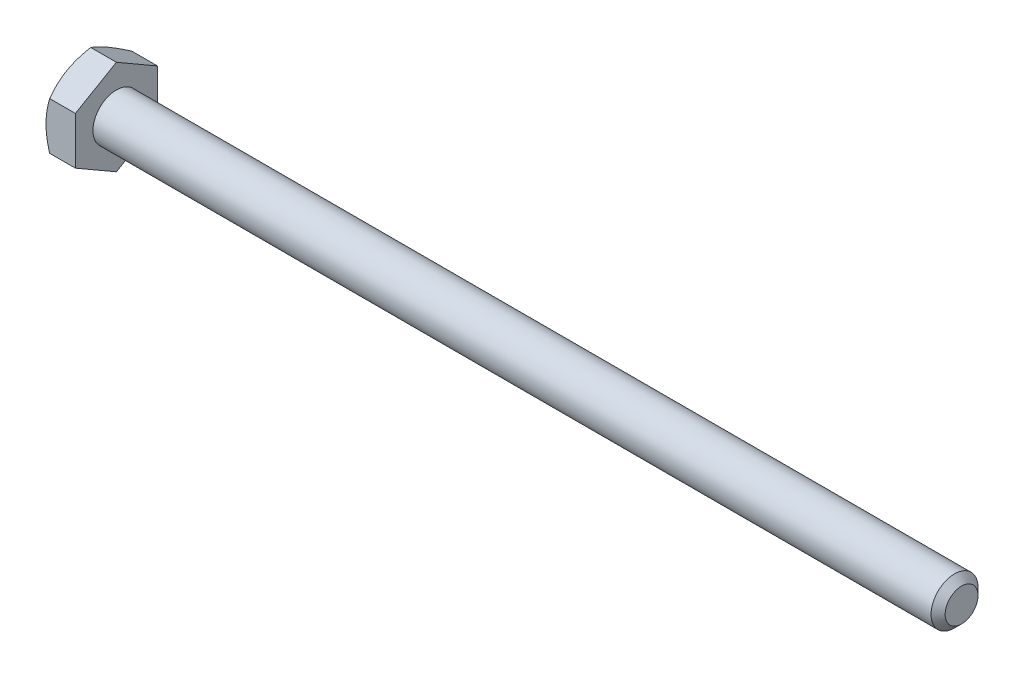
SolidWorks part; units mm, degrees
ref_plane "Front Plane" through (0, 0, 0) normal (0, 0, 1) x (1, 0, 0)
ref_plane "Top Plane" through (0, 0, 0) normal (0, 1, 0) x (1, 0, 0)
ref_plane "Right Plane" through (0, 0, 0) normal (1, 0, 0) x (0, 0, -1)
sketch "Sketch1" plane through (0, 0, 0) normal (0, 0, 1) x (1, 0, 0)
  line L0 (-59.1344, 0) -> (59.1344, 0) construction
  line L1 (59.1344, 3.175) -> (59.1344, -3.175) construction
  line L2 (-55.1656, 5.5562) -> (-55.1656, -5.5562) construction
  line L3 (-59.1344, 5.5562) -> (-59.1344, -5.5562) construction
  point P9 (-55.1656, 0)
  point P10 (54.6894, -3.175)
  dimension "D1" = 4.445
  dimension "Screw Dia" = 6.35
  dimension "Hex" = 11.1125
  dimension "Head Ht" = 3.9688
  dimension "Screw Lenght" = 114.3
ref_plane "Plane2" through (59.1344, 0, 0) normal (1, 0, 0) x (0, 0, -1)
sketch "Sketch5" plane through (59.1344, 0, 0) normal (1, 0, 0) x (0, 0, -1)
  circle A0 centre (0, 0) radius 3.175
extrude "Boss-Extrude3" add sketch "Sketch5" against normal up to vertex (114.3 mm away) up to point (-55.1656, 0, 0)
sketch "Sketch9" plane through (59.1344, 0, 0) normal (1, 0, 0) x (0, 0, -1)
  circle A1 centre (0, 0) radius 3.175
  circle A2 centre (0, 0) radius 3.175
  dimension "D1" = 0
curve "Helix/Spiral1" pitch 1.27 height 20.32 turns 16 parameters "Pitch"=1.27
chamfer "Chamfer1" distance 0.9525 angle 45 1 edges at (59.1344, 0, -3.175)
sketch "Sketch10" plane through (0, 0, 0) normal (0, 0, 1) x (1, 0, 0)
  line L0 (59.1344, 3.175) -> (59.6106, 2.3501)
  line L1 (59.6106, 2.3501) -> (59.7694, 2.3501)
  line L2 (59.7694, 2.3501) -> (60.2456, 3.175)
  line L3 (59.1344, 3.175) -> (60.2456, 3.175)
  line L4 (59.69, 3.175) -> (59.69, 2.3501) construction
  line L5 (59.3725, 2.7626) -> (60.0075, 2.7626) construction
  dimension "D1" = 60
  dimension "D2" = 0.1588
  dimension "D3" = 0.635
sketch "Sketch11" plane through (0, 0, 0) normal (0, 0, 1) x (1, 0, 0)
  line L0 (-55.1656, 3.175) -> (-55.1656, 0)
  line L1 (-55.1656, 0) -> (43.2594, 0)
  line L3 (43.2594, 0) -> (40.0844, 3.175)
  line L4 (-55.1656, 3.175) -> (40.0844, 3.175)
  dimension "D1" = 45
  dimension "MIn Thread" = 19.05
revolve "Revolve1" add sketch "Sketch11" angle 360 about L1
sketch "Sketch6" plane through (-55.1656, 0, 0) normal (-1, 0, 0) x (0, 0, 1)
  line L0 (0, 5.5562) -> (0, -5.5562) construction
  line L1 (5.5563, 3.2079) -> (0, 6.4158)
  line L2 (0, 6.4158) -> (-5.5562, 3.2079)
  line L3 (-5.5562, 3.2079) -> (-5.5562, -3.2079)
  line L4 (-5.5562, -3.2079) -> (0, -6.4158)
  line L5 (0, -6.4158) -> (5.5563, -3.2079)
  line L6 (5.5563, -3.2079) -> (5.5563, 3.2079)
  circle A0 centre (0, 0) radius 5.5563 construction
extrude "Boss-Extrude4" add sketch "Sketch6" along normal up to vertex (3.9688 mm away) up to point (-59.1344, -5.5562, 0)
sketch "Sketch7" plane through (-59.1344, 0, 0) normal (-1, 0, 0) x (0, 0, 1)
  circle A0 centre (0, 0) radius 5.5563 construction
  circle A1 centre (0, 0) radius 5.5563
sketch "Sketch8" plane through (-59.1344, 0, 0) normal (-1, 0, 0) x (0, 0, 1)
  circle A0 centre (0, 0) radius 5.5563 construction
  circle A1 centre (0, 0) radius 5.5563
extrude "Cut-Extrude3" cut sketch "Sketch8" against normal through all draft 60 flip side to cut
sketch "Sketch12" plane through (-59.1344, 0, 0) normal (-1, 0, 0) x (0, 0, 1)
  line L0 (0, 4.2783) -> (0, 2.3892) construction
  line L1 (0.1667, 4.2783) -> (0.1667, 2.3892)
  line L2 (-0.1667, 4.2783) -> (-0.1667, 2.3892)
  line L3 (0, 3.175) -> (0, -3.175) construction
  arc A0 (0.1667, 4.2783) -> (-0.1667, 4.2783) centre (0, 4.2783) ccw
  arc A1 (-0.1667, 2.3892) -> (0.1667, 2.3892) centre (0, 2.3892) ccw
  circle A3 centre (0, 0) radius 2.2225 construction
  circle A4 centre (0, 0) radius 4.445 construction
  point P2 (0, 3.3337)
  dimension "D1" = 4.445
  dimension "D3" = 8.89
  dimension "D2" = 0.3334
extrude "Cut-Extrude4" cut sketch "Sketch12" against normal blind 0.254
pattern_circular "CirPattern1" count 3 over 360 about axis through (0, 0, 0) along (1, 0, 0) of "Cut-Extrude4"
equation "\"D2@Sketch10\" = \"Pitch@Helix/Spiral1\"*.125"
equation "\"D3@Sketch10\" = \"Pitch@Helix/Spiral1\"*.5"
equation "\"D3@Helix/Spiral1\" = \"MIn Thread@Sketch11\"+\"Pitch@Helix/Spiral1\""
equation "\"D1@Chamfer1\" = \"Pitch@Helix/Spiral1\"*.75"
equation "\"D1@Sketch12\" = \"Hex@Sketch1\"*.4"
equation "\"D3@Sketch12\" = \"Hex@Sketch1\"*.8"
equation "\"D2@Sketch12\" = \"Hex@Sketch1\"*.03"
equation "\"D1@Sketch1\" = \"Pitch@Helix/Spiral1\"*3.5"
